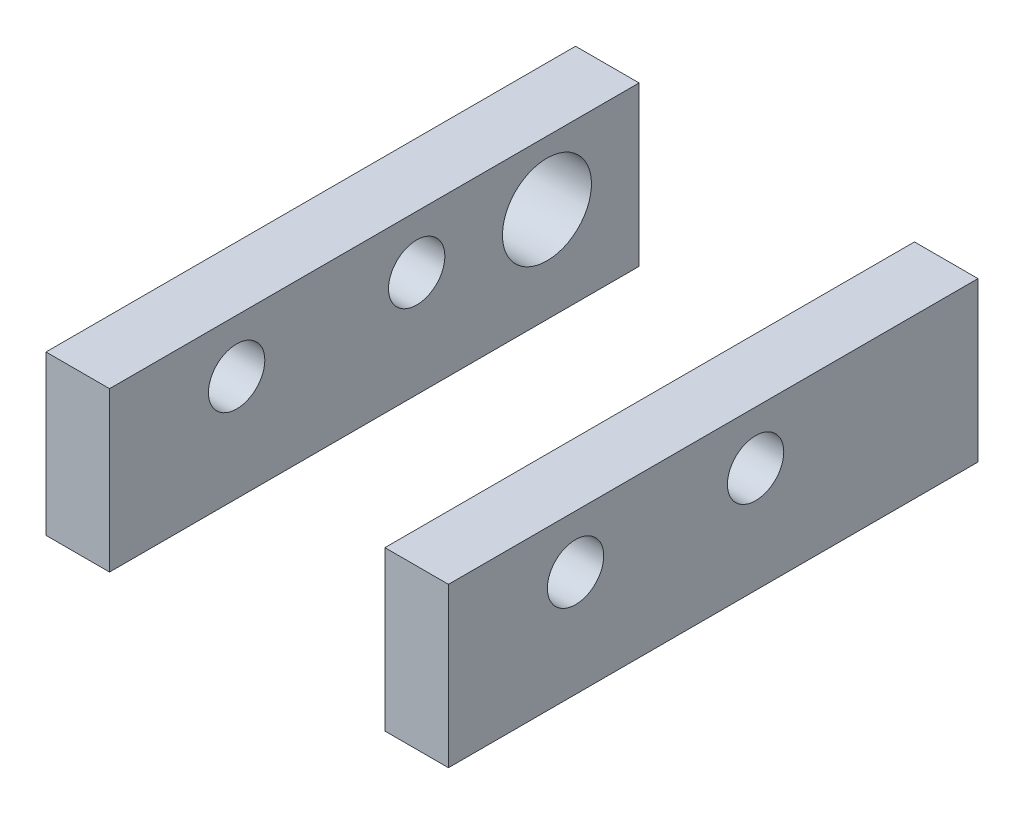
SolidWorks part; units mm, degrees
ref_plane "Front Plane" through (0, 0, 0) normal (0, 0, 1) x (1, 0, 0)
ref_plane "Top Plane" through (0, 0, 0) normal (0, 1, 0) x (1, 0, 0)
ref_plane "Right Plane" through (0, 0, 0) normal (1, 0, 0) x (0, 0, -1)
sketch "Sketch1" plane through (0, 0, 0) normal (0, 0, 1) x (1, 0, 0)
  line L0 (-7.62, 16.51) -> (0, 16.51)
  line L1 (0, 0) -> (33.02, 0)
  line L2 (0, 0) -> (0, 16.51)
  line L4 (33.02, 0) -> (33.02, 16.51)
  line L5 (-7.62, -2.54) -> (40.64, -2.54)
  line L6 (-7.62, -2.54) -> (-7.62, 16.51)
  line L8 (40.64, -2.54) -> (40.64, 16.51)
  line L9 (33.02, 16.51) -> (40.64, 16.51)
  dimension "D1" = 7.62
  dimension "D2" = 7.62
  dimension "D3" = 33.02
  dimension "D4" = 2.54
  dimension "D5" = 19.05
  dimension "D6" = 19.05
extrude "Boss-Extrude1" add sketch "Sketch1" along normal blind 63.5
sketch "Sketch2" plane through (-7.62, 0, 0) normal (-1, 0, 0) x (0, 0, 1)
  line L0 (0, 16.51) -> (0, -2.54) construction
  line L1 (63.5, 16.51) -> (0, 16.51) construction
  circle A0 centre (11.049, 8.89) radius 5.334
  dimension "D3" = 10.668
  dimension "D1" = 11.049
  dimension "D2" = 7.62
extrude "Cut-Extrude1" cut sketch "Sketch2" against normal up to next
sketch "Sketch3" plane through (40.64, 0, 0) normal (1, 0, 0) x (0, 0, -1)
  line L0 (-63.5, -2.54) -> (-63.5, 16.51) construction
  line L1 (-63.5, -2.54) -> (0, -2.54) construction
  circle A0 centre (-48.26, 10.16) radius 3.3782
  dimension "D3" = 6.7564
  dimension "D1" = 15.24
  dimension "D2" = 12.7
extrude "Cut-Extrude2" cut sketch "Sketch3" against normal through all
sketch "Sketch5" plane through (0, 0, 63.5) normal (0, 0, 1) x (1, 0, 0)
  line L0 (-7.62, -2.54) -> (40.64, -2.54) construction
  line L1 (33.02, 0) -> (0, 0) construction
  line L2 (0, -2.54) -> (33.02, -2.54)
  line L3 (33.02, 0) -> (0, 0)
  line L4 (0, 0) -> (0, -2.54)
  line L5 (33.02, 0) -> (33.02, -2.54)
extrude "Cut-Extrude4" cut sketch "Sketch5" against normal up to next and the other way through all
sketch "Sketch6" plane through (40.64, 0, 0) normal (1, 0, 0) x (0, 0, -1)
  line L0 (-63.5, -2.54) -> (-63.5, 16.51) construction
  line L1 (-63.5, 16.51) -> (0, 16.51) construction
  circle A0 centre (-26.67, 10.16) radius 3.3782
  dimension "D1" = 6.7564
  dimension "D3" = 6.35
  dimension "D2" = 36.83
extrude "Cut-Extrude5" cut sketch "Sketch6" against normal through all
